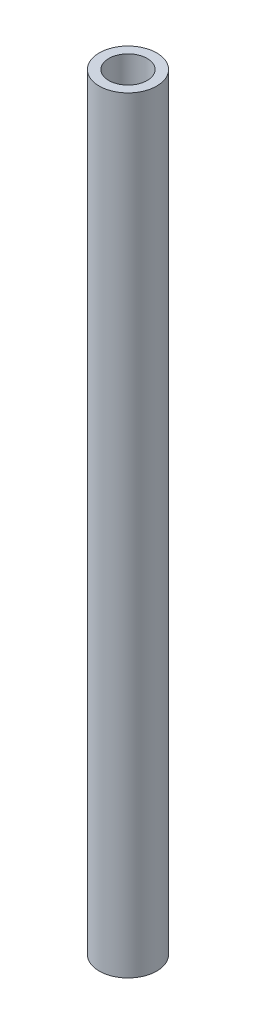
SolidWorks part; units mm, degrees
material "Malleable Cast Iron"
ref_plane "Front Plane" through (0, 0, 0) normal (0, 0, 1) x (1, 0, 0)
ref_plane "Top Plane" through (0, 0, 0) normal (0, 1, 0) x (1, 0, 0)
ref_plane "Right Plane" through (0, 0, 0) normal (1, 0, 0) x (0, 0, -1)
sketch "Sketch1" plane through (0, 0, 0) normal (0, 1, 0) x (1, 0, 0)
  circle A0 centre (0, 0) radius 15
  circle A1 centre (0, 0) radius 10
  dimension "D1" = 30
  dimension "D2" = 20
extrude "Boss-Extrude1" add sketch "Sketch1" along normal blind 400
